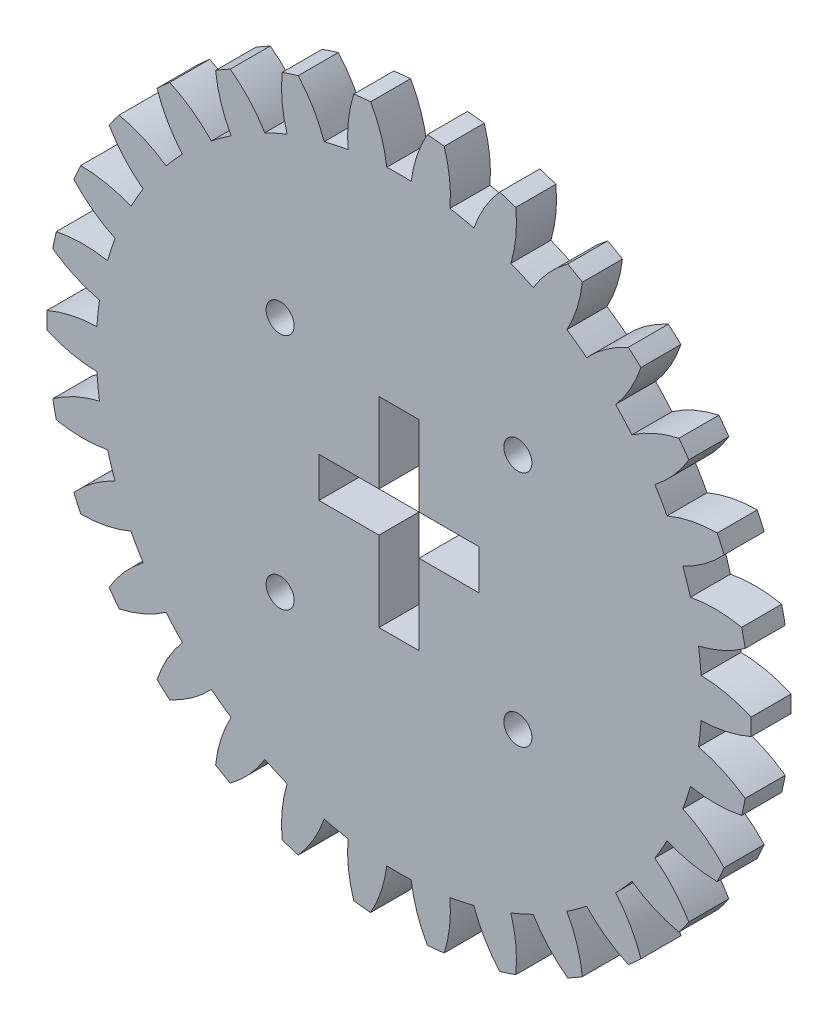
SolidWorks part; units mm, degrees
ref_plane "前视基准面" through (0, 0, 0) normal (0, 0, 1) x (1, 0, 0)
ref_plane "上视基准面" through (0, 0, 0) normal (0, 1, 0) x (1, 0, 0)
ref_plane "右视基准面" through (0, 0, 0) normal (1, 0, 0) x (0, 0, -1)
sketch "草图1" plane through (0, 0, 0) normal (0, 0, 1) x (1, 0, 0)
  arc A0 (-43.9873, -1.0569) -> (-37.7331, -2.4344) centre (-37.3786, 14.0618) ccw
  arc A1 (-37.7331, -2.4344) -> (-37.4146, -5.4639) centre (0, 0) ccw
  arc A2 (-37.4146, -5.4639) -> (-43.2458, -8.1117) centre (-33.6381, -21.5259) ccw
  arc A3 (-43.2458, -8.1117) -> (-42.8063, -10.1793) centre (0, 0) ccw
  arc A4 (-42.8063, -10.1793) -> (-36.4024, -10.2263) centre (-39.4854, 5.9831) ccw
  arc A5 (-36.4024, -10.2263) -> (-35.461, -13.1235) centre (0, 0) ccw
  arc A6 (-35.461, -13.1235) -> (-40.6143, -16.9257) centre (-28.4276, -28.0493) ccw
  arc A7 (-40.6143, -16.9257) -> (-39.7545, -18.8568) centre (0, 0) ccw
  arc A8 (-39.7545, -18.8568) -> (-33.4807, -17.5714) centre (-39.8665, -2.3572) ccw
  arc A9 (-33.4807, -17.5714) -> (-31.9576, -20.2095) centre (0, 0) ccw
  arc A10 (-31.9576, -20.2095) -> (-36.2077, -25) centre (-21.9746, -33.3468) ccw
  arc A11 (-36.2077, -25) -> (-34.9652, -26.7101) centre (0, 0) ccw
  arc A12 (-34.9652, -26.7101) -> (-29.0958, -24.1484) centre (-38.5052, -10.5943) ccw
  arc A13 (-29.0958, -24.1484) -> (-27.0575, -26.4122) centre (0, 0) ccw
  arc A14 (-27.0575, -26.4122) -> (-30.2187, -31.9817) centre (-14.5612, -37.1869) ccw
  arc A15 (-30.2187, -31.9817) -> (-28.6478, -33.3961) centre (0, 0) ccw
  arc A16 (-28.6478, -33.3961) -> (-23.4392, -29.6701) centre (-35.4611, -18.3685) ccw
  arc A17 (-23.4392, -29.6701) -> (-20.9748, -31.4606) centre (0, 0) ccw
  arc A18 (-20.9748, -31.4606) -> (-22.909, -37.5657) centre (-6.5114, -39.4017) ccw
  arc A19 (-22.909, -37.5657) -> (-21.0784, -38.6226) centre (0, 0) ccw
  arc A20 (-21.0784, -38.6226) -> (-16.7583, -33.895) centre (-30.8672, -25.3399) ccw
  arc A21 (-16.7583, -33.895) -> (-13.9754, -35.134) centre (0, 0) ccw
  arc A22 (-13.9754, -35.134) -> (-14.598, -41.5078) centre (1.8229, -39.8945) ccw
  arc A23 (-14.598, -41.5078) -> (-12.5877, -42.161) centre (0, 0) ccw
  arc A24 (-12.5877, -42.161) -> (-9.3449, -36.6385) centre (-24.9242, -31.2038) ccw
  arc A25 (-9.3449, -36.6385) -> (-6.3652, -37.2719) centre (0, 0) ccw
  arc A26 (-6.3652, -37.2719) -> (-5.649, -43.6359) centre (10.0776, -38.6437) ccw
  arc A27 (-5.649, -43.6359) -> (-3.5468, -43.8568) centre (0, 0) ccw
  arc A28 (-3.5468, -43.8568) -> (-1.5231, -37.7808) centre (-17.8919, -35.7039) ccw
  arc A29 (-1.5231, -37.7808) -> (1.5231, -37.7808) centre (0, 0) ccw
  arc A30 (1.5231, -37.7808) -> (3.5468, -43.8568) centre (17.8919, -35.7039) ccw
  arc A31 (3.5468, -43.8568) -> (5.649, -43.6359) centre (0, 0) ccw
  arc A32 (5.649, -43.6359) -> (6.3652, -37.2719) centre (-10.0776, -38.6437) ccw
  arc A33 (6.3652, -37.2719) -> (9.3449, -36.6385) centre (0, 0) ccw
  arc A34 (9.3449, -36.6385) -> (12.5877, -42.161) centre (24.9242, -31.2038) ccw
  arc A35 (12.5877, -42.161) -> (14.598, -41.5078) centre (0, 0) ccw
  arc A36 (14.598, -41.5078) -> (13.9754, -35.134) centre (-1.8229, -39.8945) ccw
  arc A37 (13.9754, -35.134) -> (16.7583, -33.895) centre (0, 0) ccw
  arc A38 (16.7583, -33.895) -> (21.0784, -38.6226) centre (30.8672, -25.3399) ccw
  arc A39 (21.0784, -38.6226) -> (22.909, -37.5657) centre (0, 0) ccw
  arc A40 (22.909, -37.5657) -> (20.9748, -31.4606) centre (6.5114, -39.4017) ccw
  arc A41 (20.9748, -31.4606) -> (23.4392, -29.6701) centre (0, 0) ccw
  arc A42 (23.4392, -29.6701) -> (28.6478, -33.3961) centre (35.4611, -18.3685) ccw
  arc A43 (28.6478, -33.3961) -> (30.2187, -31.9817) centre (0, 0) ccw
  arc A44 (30.2187, -31.9817) -> (27.0575, -26.4122) centre (14.5612, -37.1869) ccw
  arc A45 (27.0575, -26.4122) -> (29.0958, -24.1484) centre (0, 0) ccw
  arc A46 (29.0958, -24.1484) -> (34.9652, -26.7101) centre (38.5052, -10.5943) ccw
  arc A47 (34.9652, -26.7101) -> (36.2077, -25) centre (0, 0) ccw
  arc A48 (36.2077, -25) -> (31.9576, -20.2095) centre (21.9746, -33.3468) ccw
  arc A49 (31.9576, -20.2095) -> (33.4807, -17.5714) centre (0, 0) ccw
  arc A50 (33.4807, -17.5714) -> (39.7545, -18.8568) centre (39.8665, -2.3572) ccw
  arc A51 (39.7545, -18.8568) -> (40.6143, -16.9257) centre (0, 0) ccw
  arc A52 (40.6143, -16.9257) -> (35.461, -13.1235) centre (28.4276, -28.0493) ccw
  arc A53 (35.461, -13.1235) -> (36.4024, -10.2263) centre (0, 0) ccw
  arc A54 (36.4024, -10.2263) -> (42.8063, -10.1793) centre (39.4854, 5.9831) ccw
  arc A55 (42.8063, -10.1793) -> (43.2458, -8.1117) centre (0, 0) ccw
  arc A56 (43.2458, -8.1117) -> (37.4146, -5.4639) centre (33.6381, -21.5259) ccw
  arc A57 (37.4146, -5.4639) -> (37.7331, -2.4344) centre (0, 0) ccw
  arc A58 (37.7331, -2.4344) -> (43.9873, -1.0569) centre (37.3786, 14.0618) ccw
  arc A59 (43.9873, -1.0569) -> (43.9873, 1.0569) centre (0, 0) ccw
  arc A60 (43.9873, 1.0569) -> (37.7331, 2.4344) centre (37.3786, -14.0618) ccw
  arc A61 (37.7331, 2.4344) -> (37.4146, 5.4639) centre (0, 0) ccw
  arc A62 (37.4146, 5.4639) -> (43.2458, 8.1117) centre (33.6381, 21.5259) ccw
  arc A63 (43.2458, 8.1117) -> (42.8063, 10.1793) centre (0, 0) ccw
  arc A64 (42.8063, 10.1793) -> (36.4024, 10.2263) centre (39.4854, -5.9831) ccw
  arc A65 (36.4024, 10.2263) -> (35.461, 13.1235) centre (0, 0) ccw
  arc A66 (35.461, 13.1235) -> (40.6143, 16.9257) centre (28.4276, 28.0493) ccw
  arc A67 (40.6143, 16.9257) -> (39.7545, 18.8568) centre (0, 0) ccw
  arc A68 (39.7545, 18.8568) -> (33.4807, 17.5714) centre (39.8665, 2.3572) ccw
  arc A69 (33.4807, 17.5714) -> (31.9576, 20.2095) centre (0, 0) ccw
  arc A70 (31.9576, 20.2095) -> (36.2077, 25) centre (21.9746, 33.3468) ccw
  arc A71 (36.2077, 25) -> (34.9652, 26.7101) centre (0, 0) ccw
  arc A72 (34.9652, 26.7101) -> (29.0958, 24.1484) centre (38.5052, 10.5943) ccw
  arc A73 (29.0958, 24.1484) -> (27.0575, 26.4122) centre (0, 0) ccw
  arc A74 (27.0575, 26.4122) -> (30.2187, 31.9817) centre (14.5612, 37.1869) ccw
  arc A75 (30.2187, 31.9817) -> (28.6478, 33.3961) centre (0, 0) ccw
  arc A76 (28.6478, 33.3961) -> (23.4392, 29.6701) centre (35.4611, 18.3685) ccw
  arc A77 (23.4392, 29.6701) -> (20.9748, 31.4606) centre (0, 0) ccw
  arc A78 (20.9748, 31.4606) -> (22.909, 37.5657) centre (6.5114, 39.4017) ccw
  arc A79 (22.909, 37.5657) -> (21.0784, 38.6226) centre (0, 0) ccw
  arc A80 (21.0784, 38.6226) -> (16.7583, 33.895) centre (30.8672, 25.3399) ccw
  arc A81 (16.7583, 33.895) -> (13.9754, 35.134) centre (0, 0) ccw
  arc A82 (13.9754, 35.134) -> (14.598, 41.5078) centre (-1.8229, 39.8945) ccw
  arc A83 (14.598, 41.5078) -> (12.5877, 42.161) centre (0, 0) ccw
  arc A84 (12.5877, 42.161) -> (9.3449, 36.6385) centre (24.9242, 31.2038) ccw
  arc A85 (9.3449, 36.6385) -> (6.3652, 37.2719) centre (0, 0) ccw
  arc A86 (6.3652, 37.2719) -> (5.649, 43.6359) centre (-10.0776, 38.6437) ccw
  arc A87 (5.649, 43.6359) -> (3.5468, 43.8568) centre (0, 0) ccw
  arc A88 (3.5468, 43.8568) -> (1.5231, 37.7808) centre (17.8919, 35.7039) ccw
  arc A89 (1.5231, 37.7808) -> (-1.5231, 37.7808) centre (0, 0) ccw
  arc A90 (-1.5231, 37.7808) -> (-3.5468, 43.8568) centre (-17.8919, 35.7039) ccw
  arc A91 (-3.5468, 43.8568) -> (-5.649, 43.6359) centre (0, 0) ccw
  arc A92 (-5.649, 43.6359) -> (-6.3652, 37.2719) centre (10.0776, 38.6437) ccw
  arc A93 (-6.3652, 37.2719) -> (-9.3449, 36.6385) centre (0, 0) ccw
  arc A94 (-9.3449, 36.6385) -> (-12.5877, 42.161) centre (-24.9242, 31.2038) ccw
  arc A95 (-12.5877, 42.161) -> (-14.598, 41.5078) centre (0, 0) ccw
  arc A96 (-14.598, 41.5078) -> (-13.9754, 35.134) centre (1.8229, 39.8945) ccw
  arc A97 (-13.9754, 35.134) -> (-16.7583, 33.895) centre (0, 0) ccw
  arc A98 (-16.7583, 33.895) -> (-21.0784, 38.6226) centre (-30.8672, 25.3399) ccw
  arc A99 (-21.0784, 38.6226) -> (-22.909, 37.5657) centre (0, 0) ccw
  arc A100 (-22.909, 37.5657) -> (-20.9748, 31.4606) centre (-6.5114, 39.4017) ccw
  arc A101 (-20.9748, 31.4606) -> (-23.4392, 29.6701) centre (0, 0) ccw
  arc A102 (-23.4392, 29.6701) -> (-28.6478, 33.3961) centre (-35.4611, 18.3685) ccw
  arc A103 (-28.6478, 33.3961) -> (-30.2187, 31.9817) centre (0, 0) ccw
  arc A104 (-30.2187, 31.9817) -> (-27.0575, 26.4122) centre (-14.5612, 37.1869) ccw
  arc A105 (-27.0575, 26.4122) -> (-29.0958, 24.1484) centre (0, 0) ccw
  arc A106 (-29.0958, 24.1484) -> (-34.9652, 26.7101) centre (-38.5052, 10.5943) ccw
  arc A107 (-34.9652, 26.7101) -> (-36.2077, 25) centre (0, 0) ccw
  arc A108 (-36.2077, 25) -> (-31.9576, 20.2095) centre (-21.9746, 33.3468) ccw
  arc A109 (-31.9576, 20.2095) -> (-33.4807, 17.5714) centre (0, 0) ccw
  arc A110 (-33.4807, 17.5714) -> (-39.7545, 18.8568) centre (-39.8665, 2.3572) ccw
  arc A111 (-39.7545, 18.8568) -> (-40.6143, 16.9257) centre (0, 0) ccw
  arc A112 (-40.6143, 16.9257) -> (-35.461, 13.1235) centre (-28.4276, 28.0493) ccw
  arc A113 (-35.461, 13.1235) -> (-36.4024, 10.2263) centre (0, 0) ccw
  arc A114 (-36.4024, 10.2263) -> (-42.8063, 10.1793) centre (-39.4854, -5.9831) ccw
  arc A115 (-42.8063, 10.1793) -> (-43.2458, 8.1117) centre (0, 0) ccw
  arc A116 (-43.2458, 8.1117) -> (-37.4146, 5.4639) centre (-33.6381, 21.5259) ccw
  arc A117 (-37.4146, 5.4639) -> (-37.7331, 2.4344) centre (0, 0) ccw
  arc A118 (-37.7331, 2.4344) -> (-43.9873, 1.0569) centre (-37.3786, -14.0618) ccw
  arc A119 (-43.9873, 1.0569) -> (-43.9873, -1.0569) centre (0, 0) ccw
extrude "凸台-拉伸1" add sketch "草图1" along normal blind 5
sketch "草图2" plane through (0, 0, 5) normal (0, 0, 1) x (1, 0, 0)
  line L0 (0, 0) -> (14.8492, 14.8492) construction
  circle A0 centre (0, 0) radius 21 construction
  circle A1 centre (14.8492, 14.8492) radius 1.75
  circle A2 centre (14.8492, -14.8492) radius 1.75
  circle A3 centre (-14.8492, -14.8492) radius 1.75
  circle A4 centre (-14.8492, 14.8492) radius 1.75
  point P14 (0, 0)
  point P15 (0, 0)
  dimension "D1" = 42
  dimension "D2" = 3.5
  dimension "D3" = 4
extrude "切除-拉伸1" cut sketch "草图2" against normal blind 10
sketch "草图3" plane through (0, 0, 5) normal (0, 0, 1) x (1, 0, 0)
  line L0 (2.5, 2.5) -> (2.5, 12.5)
  line L1 (10, -2.5) -> (2.5, -2.5)
  line L2 (10, -2.5) -> (10, 2.5)
  line L3 (10, 2.5) -> (2.5, 2.5)
  line L4 (-10, -2.5) -> (-10, 2.5)
  line L5 (0, 2.5) -> (0, 0) construction
  line L6 (10, 0) -> (-10, 0) construction
  line L7 (-2.5, -12.5) -> (2.5, -12.5)
  line L8 (-2.5, -12.5) -> (-2.5, -2.5)
  line L9 (-2.5, 12.5) -> (2.5, 12.5)
  line L10 (2.5, -12.5) -> (2.5, -2.5)
  line L11 (0, 12.5) -> (0, 0) construction
  line L12 (-2.5, 0) -> (2.5, 0) construction
  line L13 (-2.5, 2.5) -> (-10, 2.5)
  line L14 (-2.5, 2.5) -> (-2.5, 12.5)
  line L16 (-2.5, -2.5) -> (-10, -2.5)
  point P0 (0, 0)
  point P4 (0, 0)
  dimension "D1" = 5
  dimension "D2" = 5
  dimension "D3" = 20
  dimension "D4" = 25
extrude "切除-拉伸2" cut sketch "草图3" against normal blind 10
